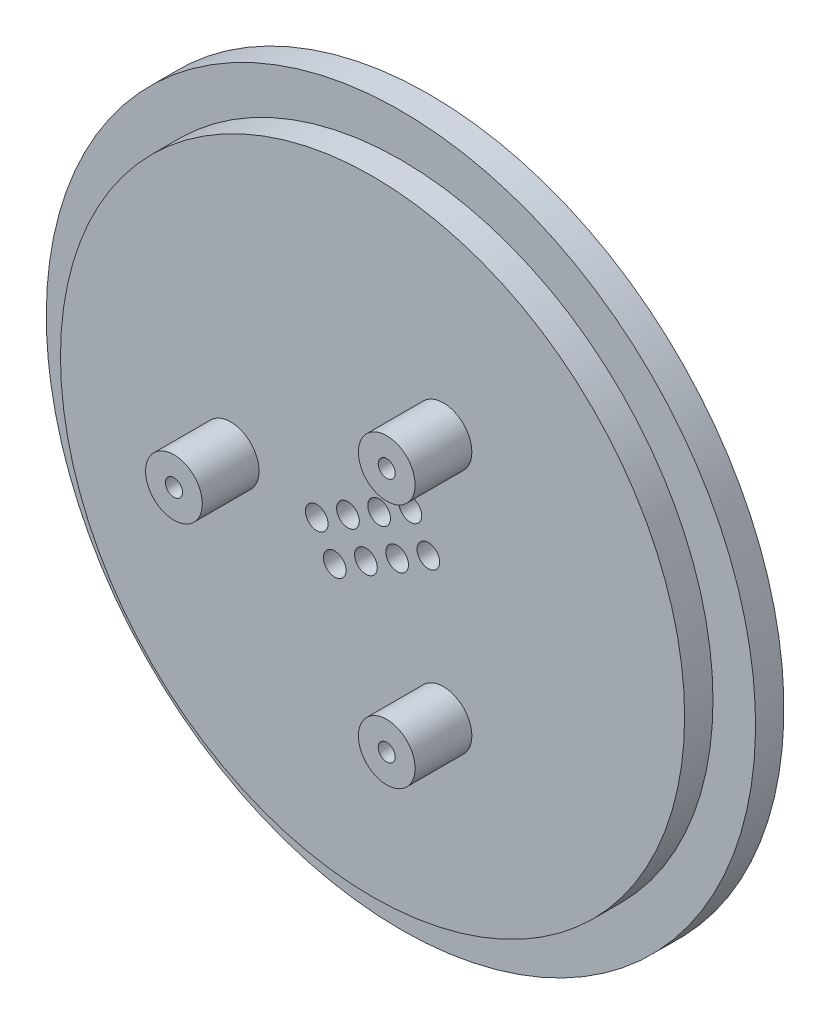
SolidWorks part; units mm, degrees
ref_plane "前视基准面" through (0, 0, 0) normal (0, 0, 1) x (1, 0, 0)
ref_plane "上视基准面" through (0, 0, 0) normal (0, 1, 0) x (1, 0, 0)
ref_plane "右视基准面" through (0, 0, 0) normal (1, 0, 0) x (0, 0, -1)
sketch "草图1" plane through (0, 0, 0) normal (0, 0, 1) x (1, 0, 0)
  circle A0 centre (0, 0) radius 22
extrude "凸台-拉伸1" add sketch "草图1" along normal blind 2
sketch "草图2" plane through (0, 0, 2) normal (0, 0, 1) x (1, 0, 0)
  circle A1 centre (-10, 0) radius 0.6
  circle A2 centre (5, -8.6603) radius 0.6
  circle A3 centre (5, 8.6603) radius 0.6
  circle A4 centre (-10, 0) radius 2
  circle A5 centre (5, 8.6603) radius 2
  circle A6 centre (5, -8.6603) radius 2
extrude "凸台-拉伸2" add sketch "草图2" along normal blind 4
sketch "草图3" plane through (0, 0, 0) normal (0, 0, -1) x (-1, 0, 0)
  circle A0 centre (0, 0) radius 25
extrude "凸台-拉伸3" add sketch "草图3" along normal blind 2
sketch "草图5" plane through (0, 0, -2) normal (0, 0, -1) x (-1, 0, 0)
  line L0 (21, -3.95) -> (21, -4)
  line L2 (21, -4) -> (29.149, -4)
  line L7 (29.149, -4) -> (29.149, 4)
  line L10 (21, -3.95) -> (21, 4)
  line L12 (29.149, 4) -> (21, 4)
extrude "切除-拉伸2" cut sketch "草图5" against normal blind 1
sketch "草图6" plane through (0, 0, -2) normal (0, 0, -1) x (-1, 0, 0)
  circle A2 centre (-18, 0) radius 5.45
  circle A3 centre (9, 15.5885) radius 5.45
  circle A4 centre (9, -15.5885) radius 5.45
  circle A5 centre (-18, 0) radius 3.85
  circle A6 centre (9, 15.5885) radius 3.85
  circle A7 centre (9, -15.5885) radius 3.85
  dimension "D1" = 3
extrude "切除-拉伸3" cut sketch "草图6" against normal blind 1.3
sketch "草图8" plane through (0, 0, 6) normal (0, 0, 1) x (1, 0, 0)
  circle A0 centre (5, -8.6603) radius 0.6
  circle A1 centre (-10, 0) radius 0.6
  circle A2 centre (5, 8.6603) radius 0.6
extrude "切除-拉伸4" cut sketch "草图8" against normal blind 18.5
sketch "草图9" plane through (0, 0, 6) normal (0, 0, 1) x (1, 0, 0)
  circle A0 centre (0, 0) radius 16.6958
extrude "切除-拉伸5" cut sketch "草图9" against normal blind 2
sketch "草图10" plane through (0, 0, -2) normal (0, 0, -1) x (-1, 0, 0)
  circle A0 centre (-5, -8.6603) radius 1.6
  circle A1 centre (-5, 8.6603) radius 1.6
extrude "切除-拉伸6" cut sketch "草图10" against normal blind 1
sketch "草图11" plane through (0, 0, -2) normal (0, 0, -1) x (-1, 0, 0)
  circle A0 centre (10, 0) radius 1.6
extrude "切除-拉伸7" cut sketch "草图11" against normal blind 3
sketch "草图13" plane through (0, 0, 4) normal (0, 0, 1) x (1, 0, 0)
  circle A0 centre (-10, 0) radius 0.6
  circle A1 centre (-10, 0) radius 2
  circle A2 centre (5, 8.6603) radius 0.6
  circle A3 centre (5, 8.6603) radius 2
  circle A4 centre (5, -8.6603) radius 0.6
  circle A5 centre (5, -8.6603) radius 2
extrude "凸台-拉伸4" add sketch "草图13" along normal blind 2
sketch "草图14" plane through (0, 0, -2) normal (0, 0, -1) x (-1, 0, 0)
  circle A2 centre (-2.6646, 3.0049) radius 0.8
  circle A3 centre (-0.4649, 1.7349) radius 0.8
  circle A4 centre (1.7349, 0.4649) radius 0.8
  circle A5 centre (3.9346, -0.8051) radius 0.8
  circle A6 centre (-1.7349, -0.4649) radius 0.8
  circle A7 centre (0.4649, -1.7349) radius 0.8
  circle A8 centre (2.6646, -3.0049) radius 0.8
  circle A9 centre (-3.9346, 0.8051) radius 0.8
  dimension "D1" = 4
  dimension "D2" = 2
extrude "切除-拉伸8" cut sketch "草图14" against normal blind 10
